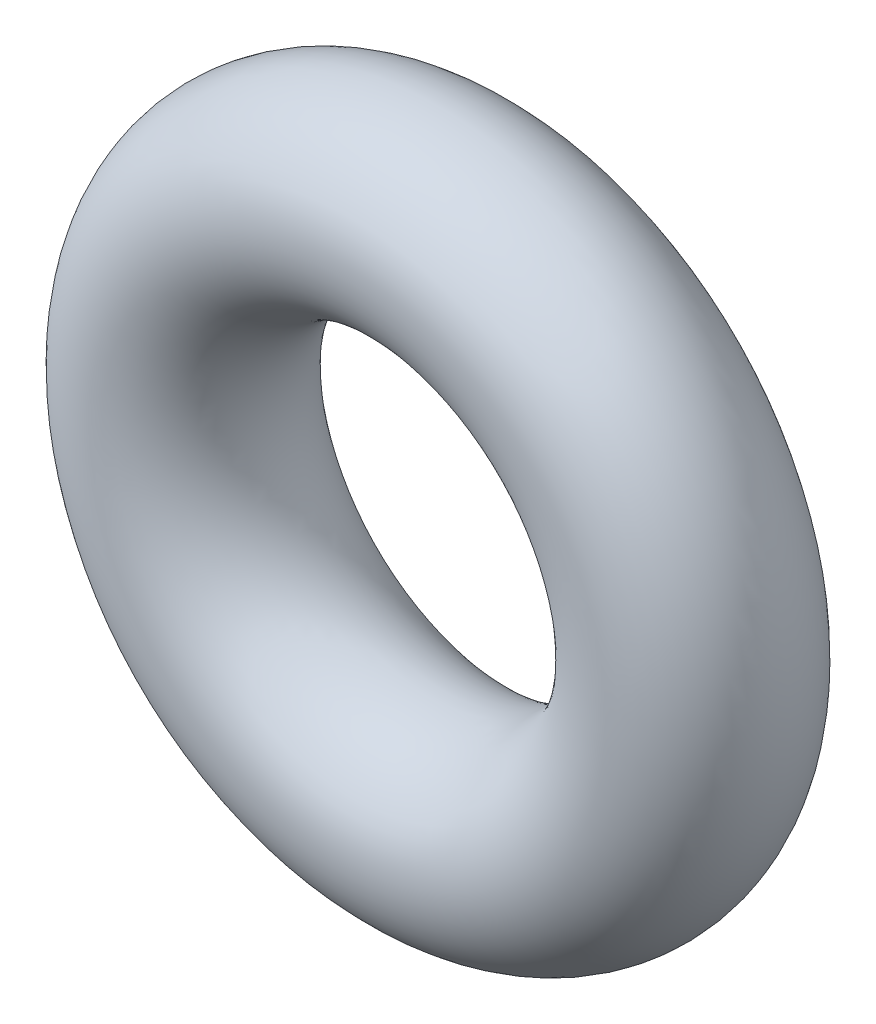
SolidWorks part; units mm, degrees
ref_plane "Front" through (0, 0, 0) normal (0, 0, 1) x (1, 0, 0)
ref_plane "Top" through (0, 0, 0) normal (0, 1, 0) x (1, 0, 0)
ref_plane "Right" through (0, 0, 0) normal (1, 0, 0) x (0, 0, -1)
sketch "Sketch1" plane through (0, 0, 0) normal (1, 0, 0) x (0, -1, 0)
  line L0 (0, -0.889) -> (0, 0.889) construction
  line L2 (-3.5484, 0) -> (3.5484, 0) construction
  line L3 (-1.4478, 0) -> (1.4478, 0) construction
  circle A0 centre (2.3368, 0) radius 0.889
  point P9 (1.4478, 0)
  point P10 (3.2258, 0)
  point P13 (2.3368, 0.889)
  point P14 (2.3368, -0.889)
  dimension "Width" = 1.778
  dimension "ID" = 2.8956
revolve "Revolve1" add sketch "Sketch1" angle 360 about L0
sketch "Sketch2" plane through (0, 0, 0) normal (0, 0, 1) x (1, 0, 0)
  circle A0 centre (0, 0) radius 0.9394
